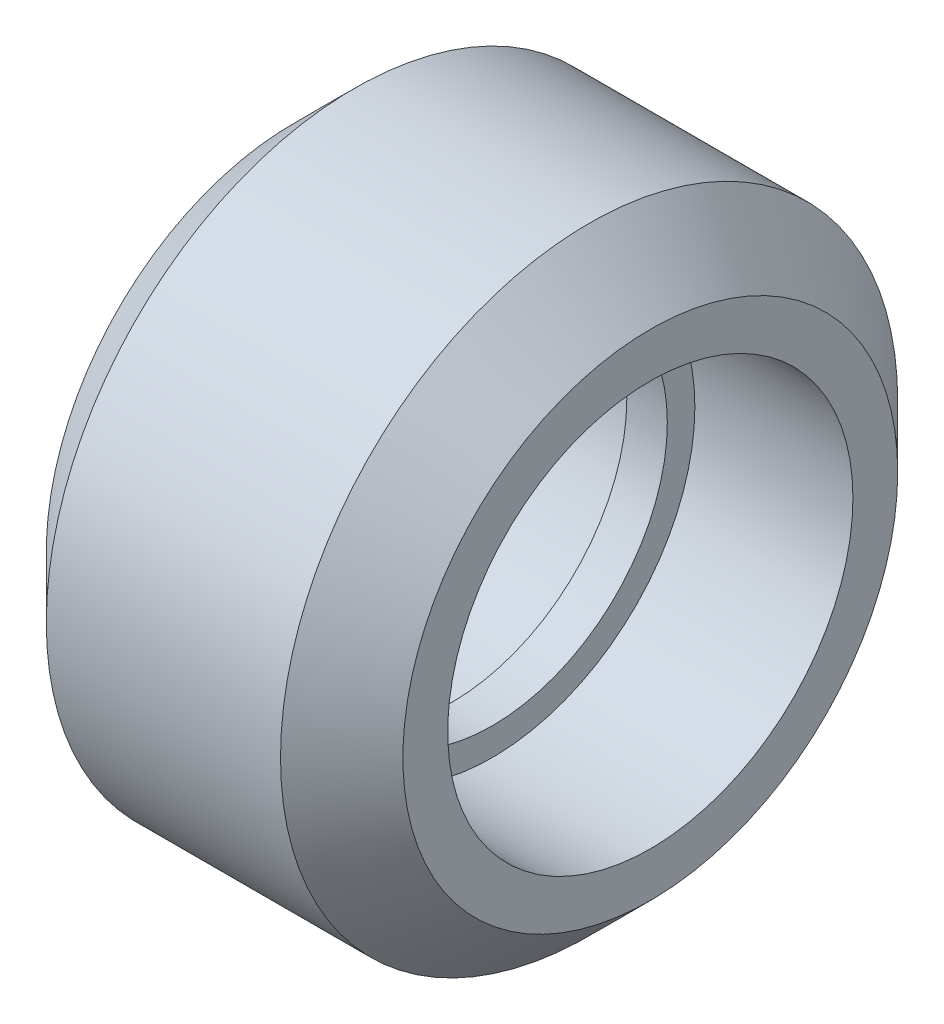
SolidWorks part; units mm, degrees
material "PC High Viscosity"
ref_plane "Front Plane" through (0, 0, 0) normal (0, 0, 1) x (1, 0, 0)
ref_plane "Top Plane" through (0, 0, 0) normal (0, 1, 0) x (1, 0, 0)
ref_plane "Right Plane" through (0, 0, 0) normal (1, 0, 0) x (0, 0, -1)
sketch "Sketch1" plane through (0, 0, 0) normal (0, 0, 1) x (1, 0, 0)
  line L0 (0.5, 4.32) -> (-0.5, 4.32)
  line L1 (-0.5, 4.32) -> (-0.5, 5)
  line L2 (-0.5, 5) -> (-4.4, 5)
  line L3 (-4.4, 5) -> (-4.4, 6.105)
  line L4 (-4.4, 6.105) -> (-2.89, 7.615)
  line L5 (-2.89, 7.615) -> (2.89, 7.615)
  line L6 (0, 7.615) -> (0, 4.32) construction
  line L7 (4.4, 6.105) -> (2.89, 7.615)
  line L8 (4.4, 5) -> (4.4, 6.105)
  line L9 (0.5, 5) -> (4.4, 5)
  line L10 (0.5, 4.32) -> (0.5, 5)
  line L11 (0, 0) -> (-12.6359, 0) construction
  dimension "D1" = 12.21
  dimension "8.64" = 8.64
  dimension "D2" = 10
  dimension "D3" = 15.23
  dimension "D4" = 1
  dimension "D5" = 45
  dimension "D6" = 8.8
  dimension "D7" = 5.78
revolve "Revolve1" add sketch "Sketch1" angle 360 about L11
